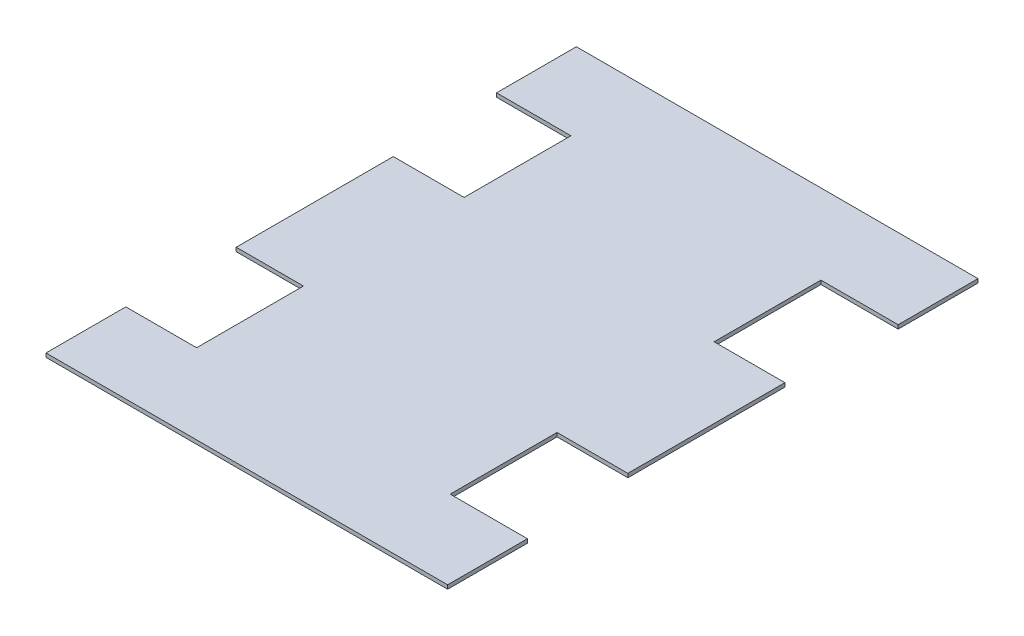
SolidWorks part; units mm, degrees
ref_plane "Front Plane" through (0, 0, 0) normal (0, 0, 1) x (1, 0, 0)
ref_plane "Top Plane" through (0, 0, 0) normal (0, 1, 0) x (1, 0, 0)
ref_plane "Right Plane" through (0, 0, 0) normal (1, 0, 0) x (0, 0, -1)
sketch "Sketch1" plane through (0, 0, 0) normal (0, 1, 0) x (1, 0, 0)
  line L25 (-27.0247, 144.779) -> (-27.0247, 206.779) construction
  line L26 (-27.0247, 144.779) -> (30.7569, 144.779) construction
  line L27 (30.7569, 61.779) -> (30.7569, 144.779) construction
  line L28 (-27.0247, 144.779) -> (-27.0247, 206.779)
  line L29 (-27.0247, 144.779) -> (30.7569, 144.779)
  line L30 (30.7569, 61.779) -> (30.7569, 144.779)
  line L31 (-27.0247, -205.221) -> (284.9753, -205.221) construction
  line L32 (-27.0247, -205.221) -> (-27.0247, -143.221) construction
  line L33 (-27.0247, -143.221) -> (27.9753, -143.221) construction
  line L34 (27.9753, -143.221) -> (27.9753, -60.221) construction
  line L35 (-24.2431, -60.221) -> (27.9753, -60.221) construction
  line L36 (-24.2431, -60.221) -> (-24.2431, 61.779) construction
  line L37 (-24.2431, 61.779) -> (30.7569, 61.779) construction
  line L38 (-27.0247, -205.221) -> (284.9753, -205.221)
  line L39 (-27.0247, -205.221) -> (-27.0247, -143.221)
  line L40 (-27.0247, -143.221) -> (27.9753, -143.221)
  line L41 (27.9753, -143.221) -> (27.9753, -60.221)
  line L42 (-24.2431, -60.221) -> (27.9753, -60.221)
  line L43 (-24.2431, -60.221) -> (-24.2431, 61.779)
  line L44 (-24.2431, 61.779) -> (30.7569, 61.779)
  line L45 (224.9717, 61.779) -> (224.9717, 144.779) construction
  line L46 (224.9717, 61.779) -> (279.9717, 61.779) construction
  line L47 (279.9717, -60.221) -> (279.9717, 61.779) construction
  line L48 (224.9717, -60.221) -> (279.9717, -60.221) construction
  line L49 (224.9717, -143.221) -> (224.9717, -60.221) construction
  line L50 (224.9717, -143.221) -> (284.9753, -143.221) construction
  line L51 (284.9753, -205.221) -> (284.9753, -143.221) construction
  line L52 (224.9717, 61.779) -> (224.9717, 144.779)
  line L53 (224.9717, 61.779) -> (279.9717, 61.779)
  line L54 (279.9717, -60.221) -> (279.9717, 61.779)
  line L55 (224.9717, -60.221) -> (279.9717, -60.221)
  line L56 (224.9717, -143.221) -> (224.9717, -60.221)
  line L57 (224.9717, -143.221) -> (284.9753, -143.221)
  line L58 (284.9753, -205.221) -> (284.9753, -143.221)
  line L59 (-27.0247, 206.779) -> (284.9753, 206.779) construction
  line L60 (284.9753, 144.779) -> (284.9753, 206.779) construction
  line L61 (224.9717, 144.779) -> (284.9753, 144.779) construction
  line L62 (-27.0247, 206.779) -> (284.9753, 206.779)
  line L63 (284.9753, 144.779) -> (284.9753, 206.779)
  line L64 (224.9717, 144.779) -> (284.9753, 144.779)
extrude "Boss-Extrude1" add sketch "Sketch1" along normal blind 3
